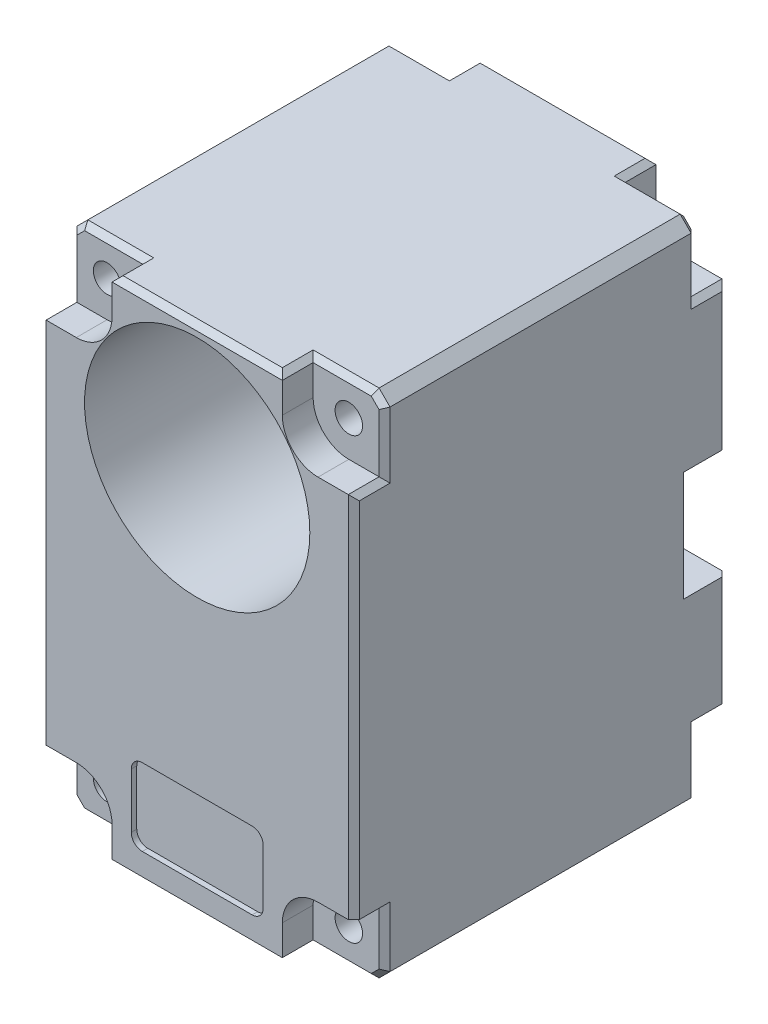
SolidWorks part; units mm, degrees
ref_plane "Front Plane" through (0, 0, 0) normal (0, 0, 1) x (1, 0, 0)
ref_plane "Top Plane" through (0, 0, 0) normal (0, 1, 0) x (1, 0, 0)
ref_plane "Right Plane" through (0, 0, 0) normal (1, 0, 0) x (0, 0, -1)
sketch "Sketch1" plane through (0, 0, 0) normal (0, 0, 1) x (1, 0, 0)
  line L1 (-14.25, 23.25) -> (14.25, 23.25)
  line L2 (-14.25, 23.25) -> (-14.25, -23.25)
  line L3 (-14.25, -23.25) -> (14.25, -23.25)
  line L4 (14.25, 23.25) -> (14.25, -23.25)
  line L5 (-14.25, 23.25) -> (14.25, -23.25) construction
  line L6 (-14.25, -23.25) -> (14.25, 23.25) construction
  point P0 (0, 0)
  dimension "D1" = 28.5
  dimension "D2" = 46.5
extrude "Boss-Extrude1" add sketch "Sketch1" along normal blind 34
sketch "Sketch2" plane through (0, 0, 34) normal (0, 0, 1) x (1, 0, 0)
  line L0 (14.25, 23.25) -> (-14.25, 23.25) construction
  line L1 (-14.25, 23.25) -> (-14.25, -23.25) construction
  circle A0 centre (0, 12) radius 10.25
  dimension "D1" = 11.25
  dimension "D2" = 20.5
  dimension "D3" = 14.25
extrude "Cut-Extrude1" cut sketch "Sketch2" against normal through all
sketch "Sketch3" plane through (0, 0, 34) normal (0, 0, 1) x (1, 0, 0)
  line L0 (-14.25, 23.25) -> (-14.25, -23.25) construction
  line L1 (14.25, 23.25) -> (-14.25, 23.25) construction
  circle A0 centre (-11, 20) radius 1.25
  circle A1 centre (11, 20) radius 1.25
  circle A2 centre (11, -20) radius 1.25
  circle A3 centre (-11, -20) radius 1.25
  dimension "D1" = 2.5
  dimension "D2" = 3.25
  dimension "D3" = 3.25
  dimension "D4" = 2
  dimension "D5" = 2
extrude "Cut-Extrude2" cut sketch "Sketch3" against normal blind 10
sketch "Sketch4" plane through (0, 0, 34) normal (0, 0, 1) x (1, 0, 0)
  line L0 (-14.25, 23.25) -> (-14.25, -23.25) construction
  line L1 (-5, -20.75) -> (5, -20.75)
  line L2 (-6, -19.75) -> (-6, -14.75)
  line L3 (-5, -13.75) -> (5, -13.75)
  line L4 (6, -19.75) -> (6, -14.75)
  line L5 (-6, -20.75) -> (6, -13.75) construction
  line L6 (-6, -13.75) -> (6, -20.75) construction
  line L8 (-14.25, -23.25) -> (14.25, -23.25) construction
  arc A0 (6, -14.75) -> (5, -13.75) centre (5, -14.75) ccw
  arc A1 (6, -19.75) -> (5, -20.75) centre (5, -19.75) cw
  arc A2 (-6, -19.75) -> (-5, -20.75) centre (-5, -19.75) ccw
  arc A3 (-6, -14.75) -> (-5, -13.75) centre (-5, -14.75) cw
  point P0 (0, -17.25)
  dimension "D5" = 1
  dimension "D1" = 12
  dimension "D2" = 8.25
  dimension "D3" = 2.5
  dimension "D4" = 7
extrude "Cut-Extrude3" cut sketch "Sketch4" against normal blind 0.5
sketch "Sketch5" plane through (0, 0, 34) normal (0, 0, 1) x (1, 0, 0)
  line L0 (0, 0) -> (5.2612, 0) construction
  line L1 (-14.25, 23.25) -> (-7.75, 23.25)
  line L2 (-14.25, 23.25) -> (-14.25, 20)
  line L3 (-14.25, 20) -> (-7.75, 20)
  line L4 (-7.75, 23.25) -> (-7.75, 20)
  line L5 (-11, 16.75) -> (-14.25, 16.75)
  line L6 (-11, 16.75) -> (-11, 20)
  line L7 (-11, 20) -> (-14.25, 20)
  line L8 (-14.25, 16.75) -> (-14.25, 20)
  line L9 (5.2612, 0) -> (0, 0) construction
  line L10 (0, 0) -> (0, 5.6616) construction
  line L11 (14.25, 16.75) -> (14.25, 20)
  line L12 (11, 16.75) -> (11, 20)
  line L13 (11, 16.75) -> (14.25, 16.75)
  line L14 (11, 20) -> (14.25, 20)
  line L15 (7.75, 23.25) -> (7.75, 20)
  line L16 (14.25, 23.25) -> (14.25, 20)
  line L17 (14.25, 23.25) -> (7.75, 23.25)
  line L18 (14.25, 20) -> (7.75, 20)
  line L19 (14.25, -20) -> (7.75, -20)
  line L20 (14.25, -23.25) -> (7.75, -23.25)
  line L21 (14.25, -23.25) -> (14.25, -20)
  line L22 (7.75, -23.25) -> (7.75, -20)
  line L23 (11, -20) -> (14.25, -20)
  line L24 (11, -16.75) -> (14.25, -16.75)
  line L25 (11, -16.75) -> (11, -20)
  line L26 (14.25, -16.75) -> (14.25, -20)
  line L27 (-14.25, -16.75) -> (-14.25, -20)
  line L28 (-11, -20) -> (-14.25, -20)
  line L29 (-11, -16.75) -> (-11, -20)
  line L30 (-11, -16.75) -> (-14.25, -16.75)
  line L31 (-7.75, -23.25) -> (-7.75, -20)
  line L32 (-14.25, -20) -> (-7.75, -20)
  line L33 (-14.25, -23.25) -> (-14.25, -20)
  line L34 (-14.25, -23.25) -> (-7.75, -23.25)
  circle A0 centre (11, -20) radius 3.25
  circle A1 centre (-11, -20) radius 3.25
  circle A2 centre (-11, 20) radius 3.25
  circle A3 centre (11, 20) radius 3.25
  circle M14 centre (-11, -20) radius 1.25
  circle M15 centre (11, -20) radius 1.25
  circle M16 centre (11, 20) radius 1.25
  circle M17 centre (-11, 20) radius 1.25
  line M19 (14.25, -23.25) -> (14.25, 23.25)
  line M20 (14.25, 23.25) -> (-14.25, 23.25)
  line M21 (-14.25, 23.25) -> (-14.25, -23.25)
  line M22 (-14.25, -23.25) -> (14.25, -23.25)
  dimension "D1" = 2
  dimension "D2" = 2
extrude "Cut-Extrude4" cut sketch "Sketch5" against normal blind 2.8 contours A2 L4 M20 | A2 L1 M21 | A2 L5 M21 | L6 A2 L3 M17 | L3 A2 L6 M17 | L3 A2 M17 | A3 L17 L15 | A3 M19 M20 | A3 L13 M19 | L18 A3 L12 M16 | L12 A3 L14 M16 | L14 A3 L18 M16 | L32 A1 L29 M14 | L28 A1 L32 M14 | L29 A1 L28 M14 | A1 L30 M21 | A1 M21 M22 | A1 L34 L31 | A0 L22 M22 | L19 A0 M15 | A0 L20 M19 | L19 A0 L25 M15 | L25 A0 L19 M15 | A0 L24 M19
ref_plane "Plane1" through (0, 0, 17) normal (0, 0, 1) x (1, 0, 0)
mirror "Mirror1" about plane through (0, 0, 17) normal (0, 0, 1) of "Cut-Extrude4"
mirror "Mirror2" about plane through (0, 0, 17) normal (0, 0, 1) of "Cut-Extrude2"
sketch "Sketch6" plane through (0, 0, 0) normal (0, 0, -1) x (-1, 0, 0)
  line L0 (-14.25, -16.75) -> (-14.25, 16.75) construction
  line L1 (-14.25, 3.75) -> (14.25, 3.75)
  line L2 (-14.25, 3.75) -> (-14.25, -6.25)
  line L3 (-14.25, -6.25) -> (14.25, -6.25)
  line L4 (14.25, 3.75) -> (14.25, -6.25)
  line L5 (14.25, 16.75) -> (14.25, -16.75) construction
  line L6 (7.75, -23.25) -> (-7.75, -23.25) construction
  dimension "D1" = 10
  dimension "D2" = 17
extrude "Cut-Extrude5" cut sketch "Sketch6" against normal blind 4
chamfer "Chamfer1" distance 1 angle 45 4 edges at (14.25, -23.25, 17) (-14.25, -23.25, 17) (-14.25, 23.25, 17) (14.25, 23.25, 17)
chamfer "Chamfer2" distance 0.5 angle 45 12 edges at (-14.25, 10.25, 0) (-14.25, 16.75, 1.4) (-14.25, 19.5, 2.8) (-13.75, 22.75, 2.8) (-10.5, 23.25, 2.8) (14.25, 10.25, 0) (0, 23.25, 0) (7.75, 23.25, 1.4) (14.25, 16.75, 1.4) (14.25, 19.5, 2.8) (13.75, 22.75, 2.8) (10.5, 23.25, 2.8)
chamfer "Chamfer3" distance 0.5 angle 45 36 edges at (-9.9164, 3.75, 0) (9.9164, 3.75, 0) (-14.25, -11.5, 0) (-14.25, -19.5, 2.8) (-13.75, -22.75, 31.2) (-13.75, -22.75, 2.8) (-10.5, -23.25, 2.8) (-7.75, -23.25, 1.4) (14.25, -11.5, 0) (14.25, -16.75, 1.4) (0, -23.25, 0) (7.75, -23.25, 1.4) (10.5, -23.25, 2.8) (14.25, -19.5, 2.8) (13.75, -22.75, 31.2) (13.75, -22.75, 2.8) (-14.25, -19.5, 31.2) (-10.5, -23.25, 31.2) (-7.75, -23.25, 32.6) (0, -23.25, 34) (7.75, -23.25, 32.6) (14.25, -19.5, 31.2) (10.5, -23.25, 31.2) (14.25, 0, 34) (14.25, 16.75, 32.6) (14.25, 19.5, 31.2) (13.75, 22.75, 31.2) (10.5, 23.25, 31.2) (7.75, 23.25, 32.6) (0, 23.25, 34) (-7.75, 23.25, 32.6) (-14.25, 0, 34) (-14.25, 16.75, 32.6) (-14.25, 19.5, 31.2) (-13.75, 22.75, 31.2) (-10.5, 23.25, 31.2)
